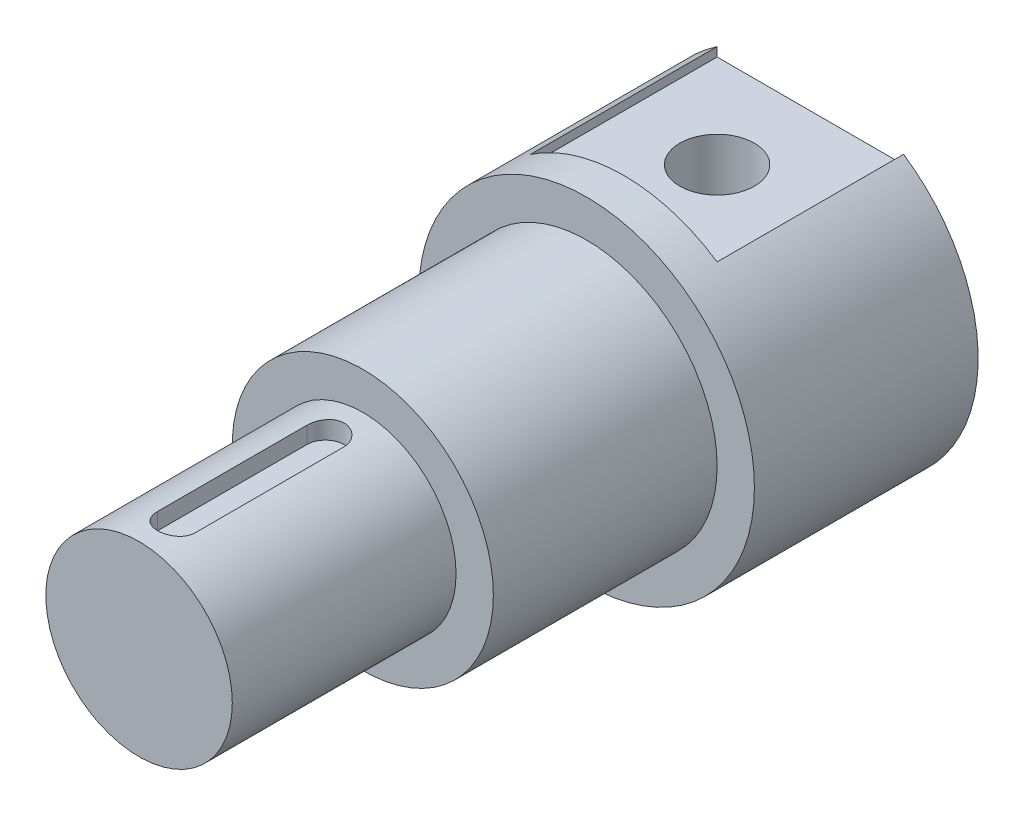
SolidWorks part; units mm, degrees
ref_plane "Alzado" through (0, 0, 0) normal (0, 0, 1) x (1, 0, 0)
ref_plane "Planta" through (0, 0, 0) normal (0, 1, 0) x (1, 0, 0)
ref_plane "Vista lateral" through (0, 0, 0) normal (1, 0, 0) x (0, 0, -1)
sketch "Croquis1" plane through (0, 0, 0) normal (0, 0, 1) x (1, 0, 0)
  circle A0 centre (0, 0) radius 18
  dimension "D1" = 36
extrude "Saliente-Extruir1" add sketch "Croquis1" along normal blind 24
sketch "Croquis2" plane through (0, 0, 24) normal (0, 0, 1) x (1, 0, 0)
  circle A0 centre (0, 0) radius 14
  dimension "D1" = 28
extrude "Saliente-Extruir2" add sketch "Croquis2" along normal blind 24
sketch "Croquis3" plane through (0, 0, 48) normal (0, 0, 1) x (1, 0, 0)
  circle A0 centre (0, 0) radius 10
  dimension "D1" = 20
extrude "Saliente-Extruir3" add sketch "Croquis3" along normal blind 24
ref_plane "Plano1" through (0, 10, 0) normal (0, 1, 0) x (1, 0, 0)
sketch "Croquis4" plane through (0, 10, 0) normal (0, 1, 0) x (1, 0, 0)
  line L0 (0, -52) -> (0, -68) construction
  line L1 (2, -52) -> (2, -68)
  line L2 (-2, -52) -> (-2, -68)
  line L3 (-10, -48) -> (10, -48) construction
  arc A0 (2, -52) -> (-2, -52) centre (0, -52) ccw
  arc A1 (-2, -68) -> (2, -68) centre (0, -68) ccw
  point P3 (0, -60)
  dimension "D1" = 2
  dimension "D2" = 16
  dimension "D3" = 12
extrude "Cortar-Extruir1" cut sketch "Croquis4" against normal blind 2
ref_plane "Plano2" through (0, -10, 0) normal (0, 1, 0) x (1, 0, 0)
sketch "Croquis5" plane through (0, -10, 0) normal (0, 1, 0) x (1, 0, 0)
  line L0 (0, -68) -> (0, -52) construction
  line L1 (-2, -68) -> (-2, -52)
  line L2 (2, -68) -> (2, -52)
  line L3 (-14, -48) -> (14, -48) construction
  arc A0 (-2, -68) -> (2, -68) centre (0, -68) ccw
  arc A1 (2, -52) -> (-2, -52) centre (0, -52) ccw
  point P3 (0, -60)
  dimension "D1" = 2
  dimension "D2" = 16
  dimension "D3" = 12
extrude "Cortar-Extruir2" cut sketch "Croquis5" along normal blind 2
ref_plane "Plano3" through (0, 18, 0) normal (0, 1, 0) x (1, 0, 0)
sketch "Croquis6" plane through (0, 18, 0) normal (0, 1, 0) x (1, 0, 0)
  line L0 (18, 0) -> (-18, 0) construction
  line L1 (-10, 0) -> (10, 0)
  line L2 (-10, 0) -> (-10, -20)
  line L3 (-10, -20) -> (10, -20)
  line L4 (10, 0) -> (10, -20)
  line L5 (-14, -24) -> (14, -24) construction
  dimension "D1" = 4
  dimension "D2" = 10
  dimension "D3" = 10
extrude "Cortar-Extruir3" cut sketch "Croquis6" against normal blind 4
ref_plane "Plano4" through (0, -18, 0) normal (0, 1, 0) x (1, 0, 0)
sketch "Croquis7" plane through (0, -18, 0) normal (0, 1, 0) x (1, 0, 0)
  line L0 (18, 0) -> (-18, 0) construction
  line L1 (-10, 0) -> (10, 0)
  line L2 (-10, 0) -> (-10, -20)
  line L3 (-10, -20) -> (10, -20)
  line L4 (10, 0) -> (10, -20)
  line L5 (-18, -24) -> (18, -24) construction
  dimension "D1" = 4
  dimension "D2" = 10
  dimension "D3" = 10
extrude "Cortar-Extruir4" cut sketch "Croquis7" along normal blind 4
sketch "Croquis8" plane through (0, -14, 0) normal (0, -1, 0) x (1, 0, 0)
  line L0 (-10, 20) -> (10, 20) construction
  line L1 (10, 0) -> (10, 20) construction
  circle A0 centre (0, 10) radius 4
  dimension "D1" = 8
  dimension "D2" = 10
  dimension "D3" = 10
extrude "Cortar-Extruir5" cut sketch "Croquis8" against normal through all
